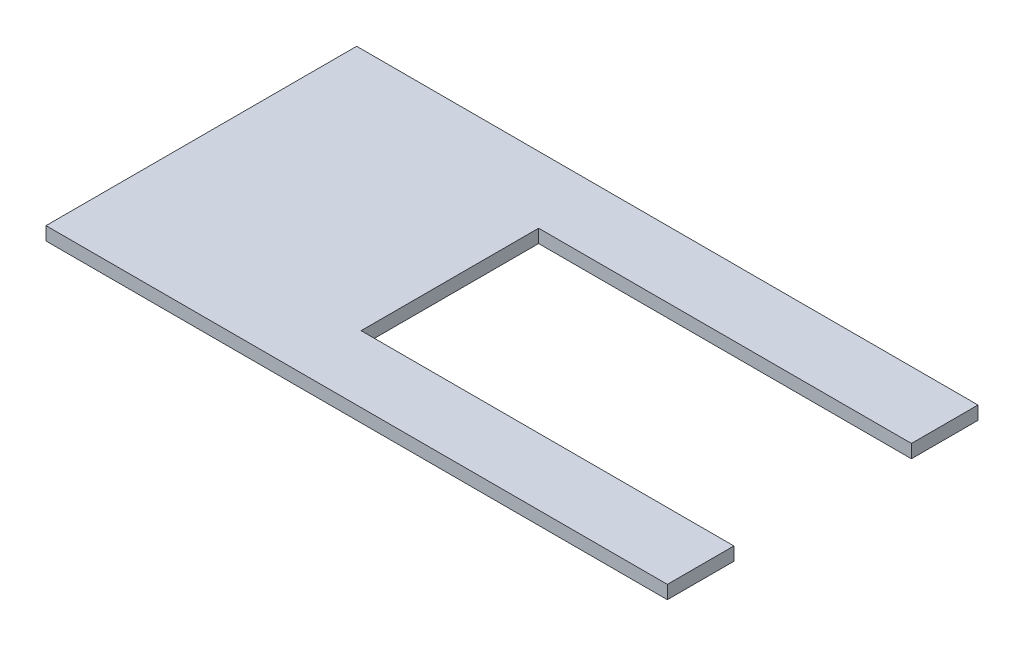
SolidWorks part; units mm, degrees
ref_plane "Front Plane" through (0, 0, 0) normal (0, 0, 1) x (1, 0, 0)
ref_plane "Top Plane" through (0, 0, 0) normal (0, 1, 0) x (1, 0, 0)
ref_plane "Right Plane" through (0, 0, 0) normal (1, 0, 0) x (0, 0, -1)
sketch "Sketch1" plane through (0, 0, 0) normal (0, 1, 0) x (1, 0, 0)
  line L1 (-35, -17.5) -> (35, -17.5)
  line L2 (-35, -17.5) -> (-35, 17.5)
  line L3 (-35, 17.5) -> (35, 17.5)
  line L4 (35, -17.5) -> (35, 17.5)
  line L5 (-35, -17.5) -> (35, 17.5) construction
  line L6 (-35, 17.5) -> (35, -17.5) construction
  line L7 (-7, -10) -> (35, -10)
  line L8 (-7, -10) -> (-7, 10)
  line L9 (-7, 10) -> (35, 10)
  line L10 (35, -10) -> (35, 10)
  line L11 (-7, -10) -> (35, 10) construction
  line L12 (-7, 10) -> (35, -10) construction
  point P0 (0, 0)
  point P6 (14, 0)
  dimension "D1" = 70
  dimension "D2" = 35
  dimension "D3" = 20
  dimension "D4" = 42
extrude "Boss-Extrude1" add sketch "Sketch1" along normal blind 1.5 contours L8 L9 L4 L3 L2 L1 L7
